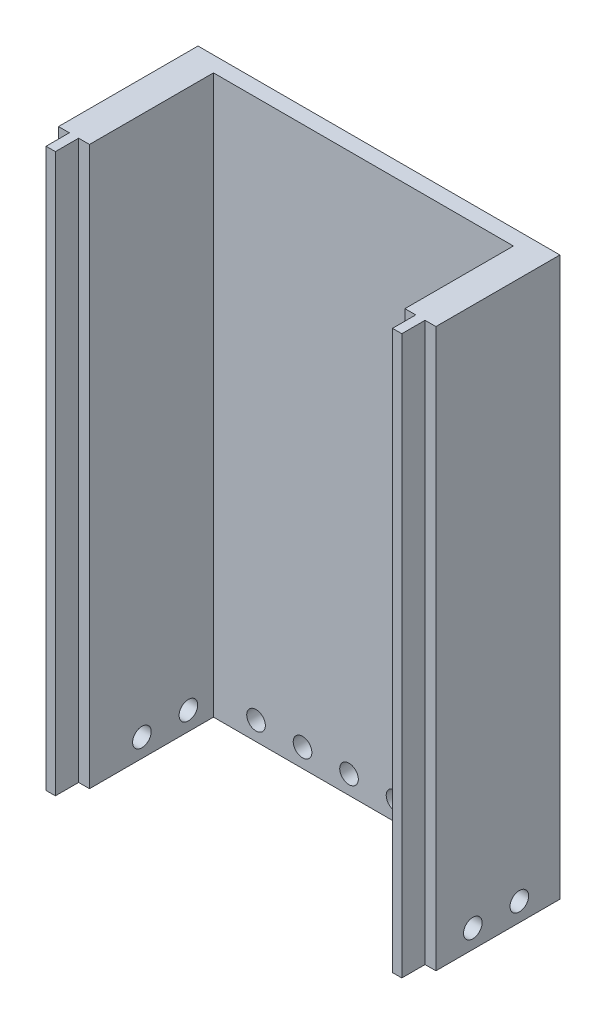
SolidWorks part; units mm, degrees
material "Polyetheretherketone (PEEK)"
ref_plane "Ebene vorne" through (0, 0, 0) normal (0, 0, 1) x (1, 0, 0)
ref_plane "Ebene oben" through (0, 0, 0) normal (0, 1, 0) x (1, 0, 0)
ref_plane "Ebene rechts" through (0, 0, 0) normal (1, 0, 0) x (0, 0, -1)
sketch "Sketch1" plane through (0, 0, 0) normal (0, 1, 0) x (1, 0, 0)
  line L0 (-8.3723, -12.1909) -> (-8.3723, -16.6909)
  line L1 (-8.3723, -16.6909) -> (-8.0223, -16.6909)
  line L2 (-7.3723, -16.6909) -> (-7.3723, -12.6909)
  line L3 (2.3027, -12.6909) -> (2.3027, -16.1909)
  line L4 (-8.0223, -16.6909) -> (-8.0223, -17.4409)
  line L5 (3.3027, -16.1909) -> (3.3027, -12.1909)
  line L6 (-7.3723, -12.6909) -> (2.3027, -12.6909)
  line L7 (-8.3723, -12.1909) -> (3.3027, -12.1909)
  line L8 (-8.0223, -17.4409) -> (-7.7223, -17.4409)
  line L9 (-7.7223, -17.4409) -> (-7.7223, -16.6909)
  line L10 (-7.7223, -16.6909) -> (-7.3723, -16.6909)
  line L11 (2.3027, -16.1909) -> (2.6527, -16.1909)
  line L12 (2.6527, -16.1909) -> (2.6527, -16.9409)
  line L13 (2.6527, -16.9409) -> (2.9527, -16.9409)
  line L14 (2.9527, -16.9409) -> (2.9527, -16.1909)
  line L15 (2.9527, -16.1909) -> (3.3027, -16.1909)
  line L16 (2.9527, -16.1909) -> (3.8816, -16.1909) construction
  line L17 (2.6527, -16.9409) -> (2.6527, -16.1909) construction
  line L18 (1.7238, -16.1909) -> (2.6527, -16.1909) construction
  line L19 (-7.0703, -16.6909) -> (-7.7223, -16.6909) construction
  line L20 (-7.7223, -16.6909) -> (-7.7223, -17.4409) construction
  line L21 (-8.0223, -16.6909) -> (-8.0223, -17.4409) construction
  line L22 (-8.0223, -16.6909) -> (-8.6683, -16.6909) construction
  dimension "D2" = 1
  dimension "D3" = 0.5
  dimension "D5" = 4
  dimension "D6" = 1
extrude "Boss-Extrude1" add sketch "Sketch1" along normal blind 18
sketch "Sketch5" plane through (0, 0, 12.6909) normal (0, 0, 1) x (1, 0, 0)
  circle A0 centre (-6, 0.6) radius 0.3
  circle A1 centre (-4.5, 0.6) radius 0.3
  circle A2 centre (-3, 0.6) radius 0.3
  circle A3 centre (-1.5, 0.6) radius 0.3
  circle A4 centre (1.5, 0.6) radius 0.3
  circle A5 centre (0, 0.6) radius 0.3
extrude "Cut-Extrude1" cut sketch "Sketch5" against normal through all
sketch "Sketch6" plane through (3.3027, 0, 0) normal (1, 0, 0) x (0, 0, -1)
  circle A0 centre (-15, 0.6) radius 0.3
  circle A1 centre (-13.5, 0.6) radius 0.3
extrude "Cut-Extrude2" cut sketch "Sketch6" against normal through all
